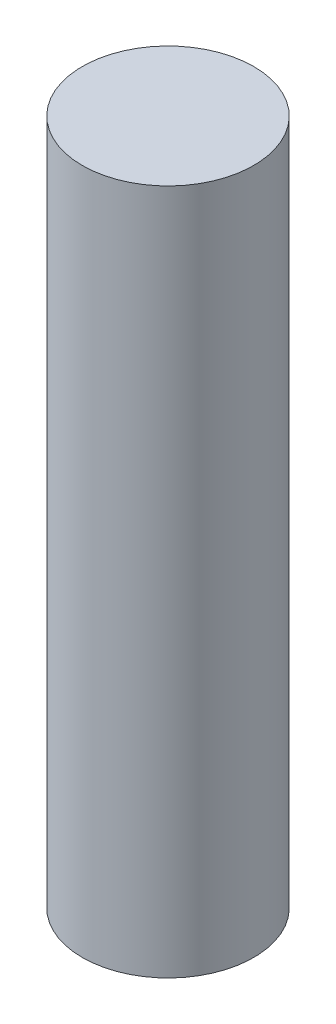
SolidWorks part; units mm, degrees
ref_plane "Ebene vorne" through (0, 0, 0) normal (0, 0, 1) x (1, 0, 0)
ref_plane "Ebene oben" through (0, 0, 0) normal (0, 1, 0) x (1, 0, 0)
ref_plane "Ebene rechts" through (0, 0, 0) normal (1, 0, 0) x (0, 0, -1)
sketch "Sketch1" plane through (0, 0, 0) normal (0, 1, 0) x (1, 0, 0)
  circle A0 centre (0, 0) radius 20
  dimension "D1" = 40
extrude "Boss-Extrude1" add sketch "Sketch1" along normal blind 160
